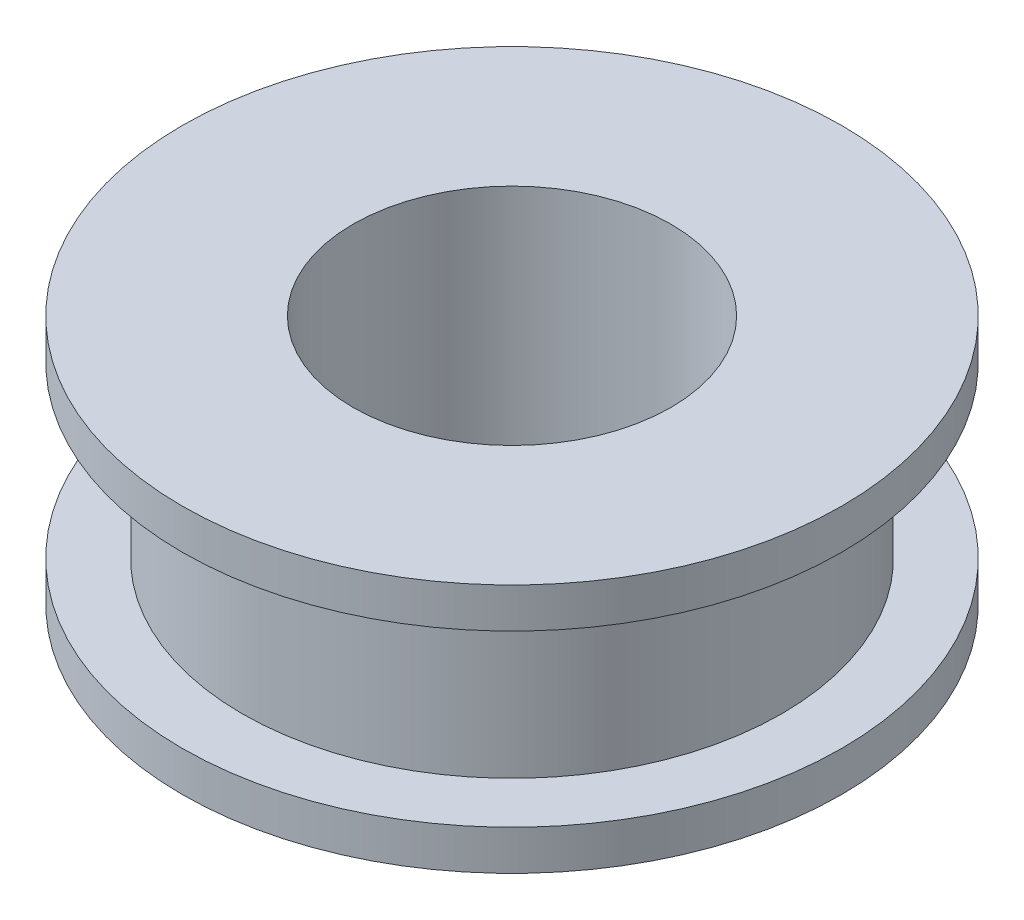
SolidWorks part; units mm, degrees
material "ABS"
ref_plane "前视基准面" through (0, 0, 0) normal (0, 0, 1) x (1, 0, 0)
ref_plane "上视基准面" through (0, 0, 0) normal (0, 1, 0) x (1, 0, 0)
ref_plane "右视基准面" through (0, 0, 0) normal (1, 0, 0) x (0, 0, -1)
sketch "草图1" plane through (0, 0, 0) normal (0, 0, 1) x (1, 0, 0)
  line L0 (0, 35.1394) -> (0, -38.2606) construction
  line L1 (-57.6, 0) -> (44.8135, 0) construction
  line L2 (16.5, 6.25) -> (7.95, 6.25)
  line L3 (-16.5, 6.25) -> (-16.5, 4.25)
  line L4 (-16.5, 4.25) -> (-13.5, 4.25)
  line L5 (-13.5, 4.25) -> (-13.5, -4.25)
  line L6 (13.5, 4.25) -> (13.5, -4.25)
  line L7 (16.5, 4.25) -> (13.5, 4.25)
  line L8 (16.5, 6.25) -> (16.5, 4.25)
  line L9 (16.5, -6.25) -> (16.5, -4.25)
  line L10 (16.5, -4.25) -> (13.5, -4.25)
  line L11 (-16.5, -4.25) -> (-13.5, -4.25)
  line L12 (-16.5, -6.25) -> (-16.5, -4.25)
  line L13 (16.5, -6.25) -> (7.95, -6.25)
  line L14 (-7.95, 6.25) -> (-7.95, -6.25)
  line L15 (7.95, 6.25) -> (7.95, -6.25)
  line L16 (-7.95, 6.25) -> (-16.5, 6.25)
  line L17 (-7.95, -6.25) -> (-16.5, -6.25)
  point P5 (0, -6)
  point P14 (0, 6)
  point P18 (13.5, 0)
  point P19 (-13.5, 0)
  dimension "D1" = 2
  dimension "D2" = 8.5
  dimension "D3" = 27
  dimension "D4" = 3
  dimension "D5" = 15.9
revolve "旋转1" add sketch "草图1" angle 360 about L0
